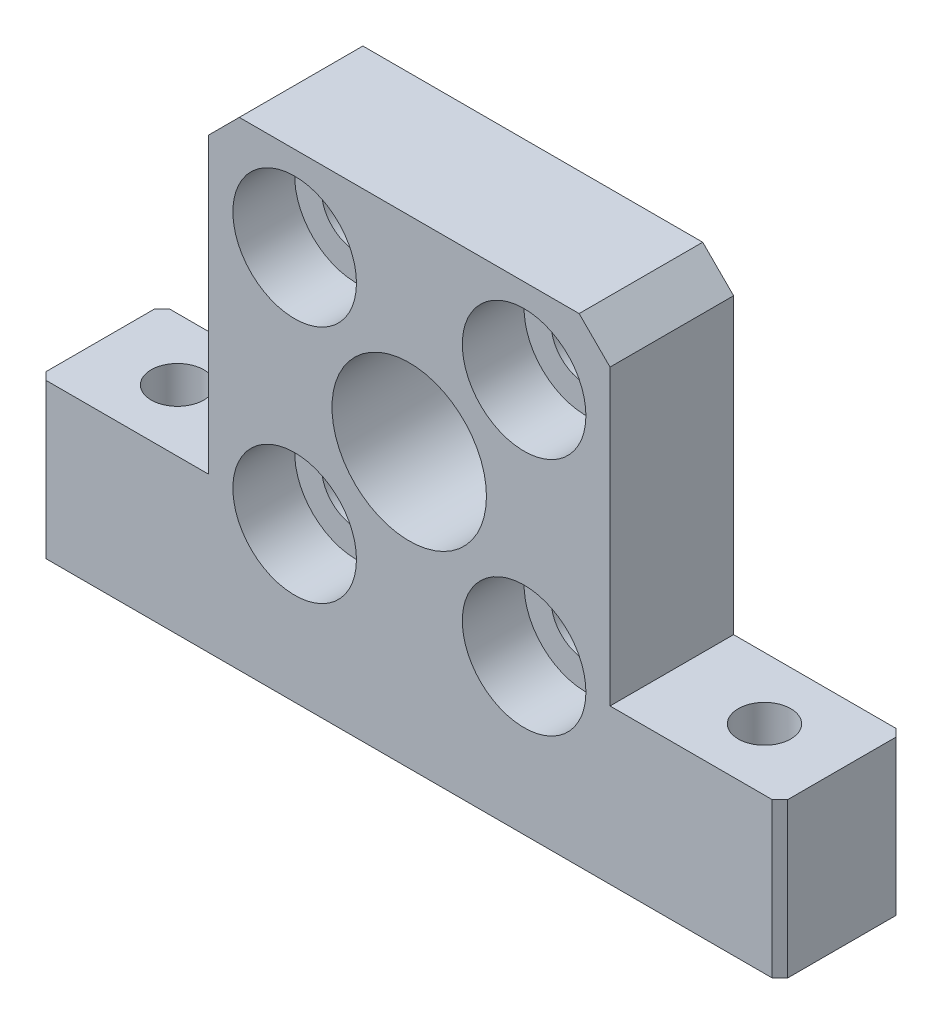
SolidWorks part; units mm, degrees
ref_plane "Front Plane" through (0, 0, 0) normal (0, 0, 1) x (1, 0, 0)
ref_plane "Top Plane" through (0, 0, 0) normal (0, 1, 0) x (1, 0, 0)
ref_plane "Right Plane" through (0, 0, 0) normal (1, 0, 0) x (0, 0, -1)
sketch "Sketch1" plane through (0, 0, 0) normal (0, 0, 1) x (1, 0, 0)
  line L0 (16.9781, -11.0195) -> (27.9781, -11.0195)
  line L1 (-9.0219, 9.9805) -> (16.9781, 9.9805)
  line L2 (-9.0219, 9.9805) -> (-9.0219, -11.0195)
  line L4 (16.9781, 9.9805) -> (16.9781, -11.0195)
  line L5 (-20.0219, -21.0195) -> (27.9781, -21.0195)
  line L6 (-20.0219, -21.0195) -> (-20.0219, -11.0195)
  line L7 (-20.0219, -11.0195) -> (-9.0219, -11.0195)
  line L8 (27.9781, -21.0195) -> (27.9781, -11.0195)
  circle A0 centre (-3.4371, -11.0195) radius 2.25
  circle A1 centre (11.4161, -11.0195) radius 2.25
  circle A2 centre (-3.4371, 4.4805) radius 2.25
  circle A3 centre (11.4161, 4.4805) radius 2.25
  circle A4 centre (3.9781, -3.2695) radius 5
  point P16 (3.9781, 9.9805)
  dimension "D7" = 4.5
  dimension "D8" = 10
  dimension "D1" = 26
  dimension "D2" = 11
  dimension "D3" = 10
  dimension "D4" = 25.5
  dimension "D5" = 31
  dimension "D6" = 10
  dimension "D9" = 17.75
extrude "Boss-Extrude1" add sketch "Sketch1" along normal blind 8
sketch "Sketch2" plane through (0, 0, 8) normal (0, 0, 1) x (1, 0, 0)
  circle A0 centre (-3.4371, 4.4805) radius 4
  circle A1 centre (11.4161, 4.4805) radius 4
  circle A2 centre (-3.4371, -11.0195) radius 4
  circle A3 centre (11.4161, -11.0195) radius 4
  dimension "D1" = 8
extrude "Cut-Extrude1" cut sketch "Sketch2" against normal blind 4
sketch "Sketch3" plane through (0, 9.9805, 0) normal (0, 1, 0) x (1, 0, 0)
  line L0 (-9.0219, -8) -> (-9.0219, 0) construction
  line L1 (-20.0219, -8) -> (-20.0219, 0) construction
  circle A0 centre (-15.0219, -4) radius 1.7016
  circle A1 centre (22.9781, -4) radius 1.7016
  point P6 (-9.0219, -4)
  dimension "D1" = 43
  dimension "D2" = 5
extrude "Cut-Extrude2" cut sketch "Sketch3" against normal through all
chamfer "Chamfer1" distance 2 angle 45 2 edges at (16.9781, 9.9805, 4) (-9.0219, 9.9805, 4)
chamfer "Chamfer2" distance 0.5 angle 45 4 edges at (27.9781, -16.0195, 8) (27.9781, -16.0195, 0) (-20.0219, -16.0195, 0) (-20.0219, -16.0195, 8)
